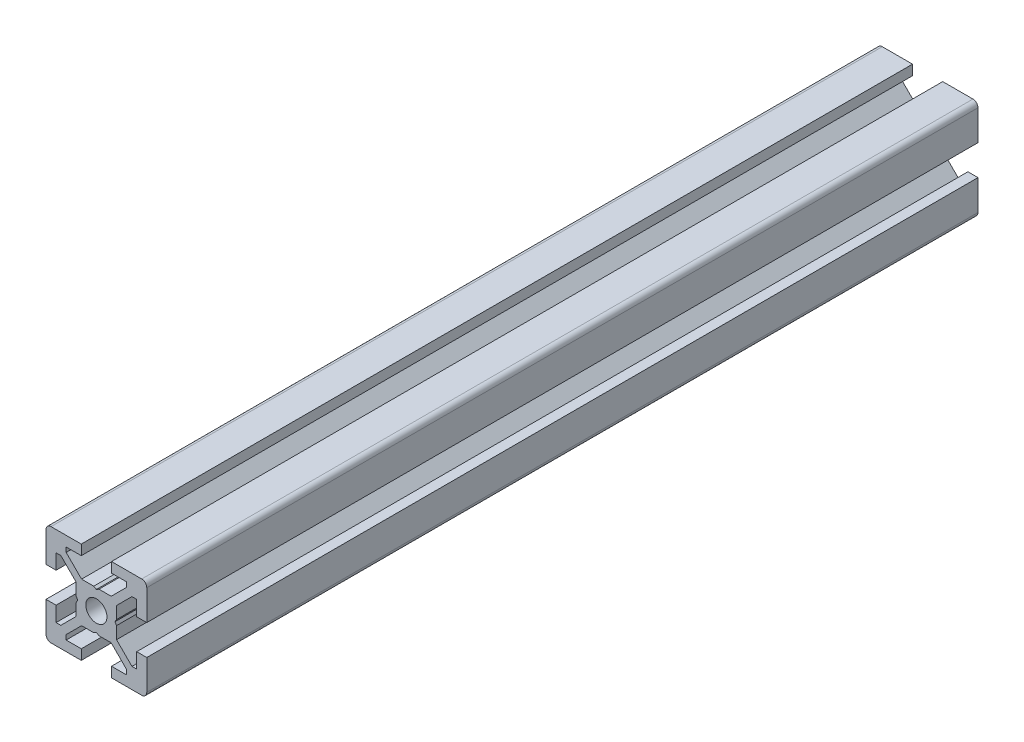
SolidWorks part; units mm, degrees
material "2014 合金"
ref_plane "正面" through (0, 0, 0) normal (0, 0, 1) x (1, 0, 0)
ref_plane "平面" through (0, 0, 0) normal (0, 1, 0) x (1, 0, 0)
ref_plane "右側面" through (0, 0, 0) normal (1, 0, 0) x (0, 0, -1)
ref_plane "平面1" through (0, 0, 0) normal (0, 0, 1) x (1, 0, 0)
sketch "ｽｹｯﾁ1" plane through (0, 0, 0) normal (0, 0, 1) x (1, 0, 0)
  line L0 (-10, -3) -> (-10, -9)
  line L1 (-9, -10) -> (-3, -10)
  line L2 (-3, -10) -> (-3, -8)
  line L3 (-3, -8) -> (-6, -8)
  line L4 (-6, -8) -> (-6, -7.0607)
  line L5 (-6, -7.0607) -> (-2.9393, -4)
  line L6 (-2.9393, -4) -> (-0.5196, -4)
  line L7 (-0.5196, -4) -> (0, -3.7)
  line L8 (0, -3.7) -> (0.5196, -4)
  line L9 (0.5196, -4) -> (2.9393, -4)
  line L10 (2.9393, -4) -> (6, -7.0607)
  line L11 (6, -7.0607) -> (6, -8)
  line L12 (6, -8) -> (3, -8)
  line L13 (3, -8) -> (3, -10)
  line L14 (3, -10) -> (9, -10)
  line L15 (10, -9) -> (10, -3)
  line L16 (10, -3) -> (8, -3)
  line L17 (8, -3) -> (8, -6)
  line L18 (8, -6) -> (7.0607, -6)
  line L19 (7.0607, -6) -> (4, -2.9393)
  line L20 (4, -2.9393) -> (4, -0.5196)
  line L21 (4, -0.5196) -> (3.7, 0)
  line L22 (3.7, 0) -> (4, 0.5196)
  line L23 (4, 0.5196) -> (4, 2.9393)
  line L24 (4, 2.9393) -> (7.0607, 6)
  line L25 (7.0607, 6) -> (8, 6)
  line L26 (8, 6) -> (8, 3)
  line L27 (8, 3) -> (10, 3)
  line L28 (10, 3) -> (10, 9)
  line L29 (9, 10) -> (3, 10)
  line L30 (3, 10) -> (3, 8)
  line L31 (3, 8) -> (6, 8)
  line L32 (6, 8) -> (6, 7.0607)
  line L33 (6, 7.0607) -> (2.9393, 4)
  line L34 (2.9393, 4) -> (0.5196, 4)
  line L35 (0.5196, 4) -> (0, 3.7)
  line L36 (0, 3.7) -> (-0.5196, 4)
  line L37 (-0.5196, 4) -> (-2.9393, 4)
  line L38 (-2.9393, 4) -> (-6, 7.0607)
  line L39 (-6, 7.0607) -> (-6, 8)
  line L40 (-6, 8) -> (-3, 8)
  line L41 (-3, 8) -> (-3, 10)
  line L42 (-3, 10) -> (-9, 10)
  line L43 (-10, 9) -> (-10, 3)
  line L44 (-10, 3) -> (-8, 3)
  line L45 (-8, 3) -> (-8, 6)
  line L46 (-8, 6) -> (-7.0607, 6)
  line L47 (-7.0607, 6) -> (-4, 2.9393)
  line L48 (-4, 2.9393) -> (-4, 0.5196)
  line L49 (-4, 0.5196) -> (-3.7, 0)
  line L50 (-3.7, 0) -> (-4, -0.5196)
  line L51 (-4, -0.5196) -> (-4, -2.9393)
  line L52 (-4, -2.9393) -> (-7.0607, -6)
  line L53 (-7.0607, -6) -> (-8, -6)
  line L54 (-8, -6) -> (-8, -3)
  line L55 (-8, -3) -> (-10, -3)
  arc A0 (-10, -9) -> (-9, -10) centre (-9, -9) ccw
  arc A1 (9, -10) -> (10, -9) centre (9, -9) ccw
  arc A2 (10, 9) -> (9, 10) centre (9, 9) ccw
  arc A3 (-9, 10) -> (-10, 9) centre (-9, 9) ccw
extrude "ﾎﾞｽ - 押し出し1" add sketch "ｽｹｯﾁ1" against normal blind 165
ref_plane "平面2" through (0, 0, 0) normal (1, 0, 0) x (0, 0, -1)
sketch "ｽｹｯﾁ2" plane through (0, 0, 0) normal (1, 0, 0) x (0, 0, -1)
  line L0 (0, 0) -> (0, 2.1)
  line L1 (0, 2.1) -> (260, 2.1)
  line L2 (260, 2.1) -> (260, 0)
  line L3 (260, 0) -> (0, 0)
  line L4 (260, 0) -> (0, 0) construction
revolve "ｶｯﾄ - 回転1" cut sketch "ｽｹｯﾁ2" angle 360 about L4
